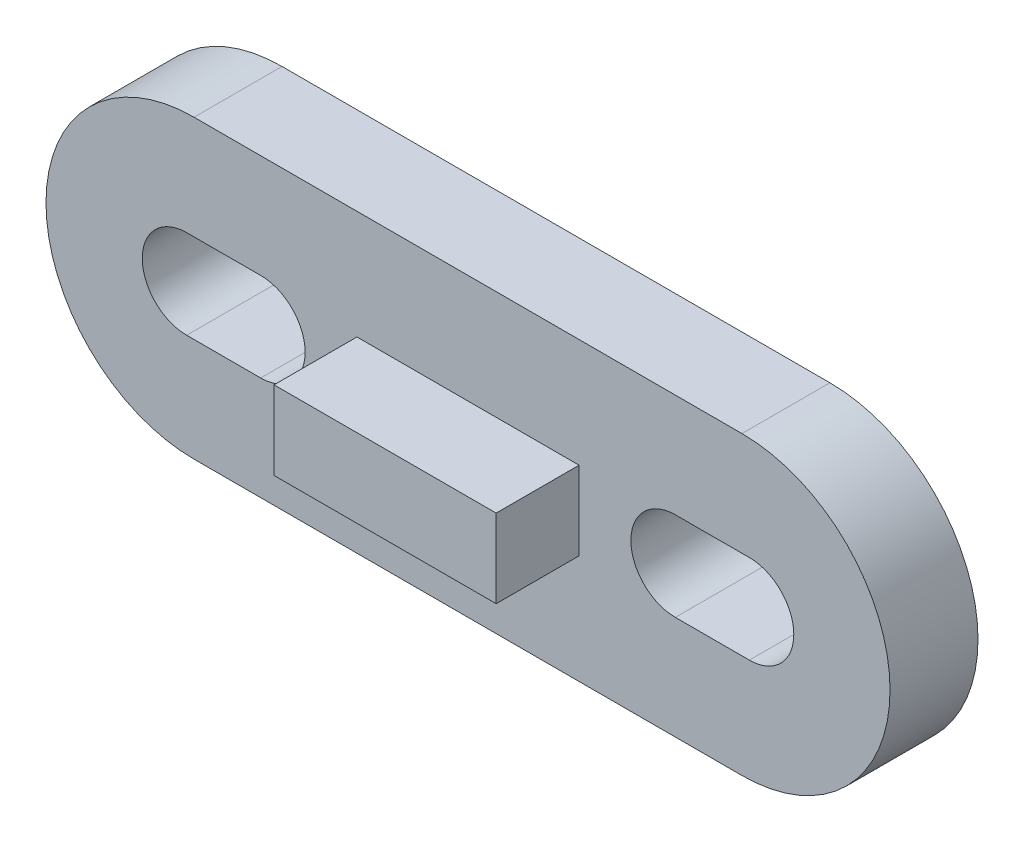
SolidWorks part; units mm, degrees
ref_plane "Front Plane" through (0, 0, 0) normal (0, 0, 1) x (1, 0, 0)
ref_plane "Top Plane" through (0, 0, 0) normal (0, 1, 0) x (1, 0, 0)
ref_plane "Right Plane" through (0, 0, 0) normal (1, 0, 0) x (0, 0, -1)
sketch "Sketch3" plane through (0, 0, 0) normal (0, 0, 1) x (1, 0, 0)
  line L0 (-9.25, 0) -> (9.25, 0) construction
  line L3 (-9.5, 0) -> (-7, 0) construction
  line L4 (-9.5, 1.5) -> (-7, 1.5)
  line L5 (-9.5, -1.5) -> (-7, -1.5)
  line L6 (9.5, 0) -> (7, 0) construction
  line L9 (-9.25, 5) -> (9.25, 5)
  line L10 (-9.25, -5) -> (9.25, -5)
  line L11 (9.5, -1.5) -> (7, -1.5)
  line L12 (9.5, 1.5) -> (7, 1.5)
  line L13 (5.5, 0) -> (-5.5, 0) construction
  arc A2 (-9.5, 1.5) -> (-9.5, -1.5) centre (-9.5, 0) ccw
  arc A3 (-7, -1.5) -> (-7, 1.5) centre (-7, 0) ccw
  arc A6 (-9.25, 5) -> (-9.25, -5) centre (-9.25, 0) ccw
  arc A7 (9.25, -5) -> (9.25, 5) centre (9.25, 0) ccw
  arc A8 (9.5, -1.5) -> (9.5, 1.5) centre (9.5, 0) ccw
  arc A9 (7, 1.5) -> (7, -1.5) centre (7, 0) ccw
  point P2 (0, 0)
  point P10 (-8.25, 0)
  point P16 (8.25, 0)
  point P21 (0, 0)
  point P23 (-5.5, 0)
  dimension "D2" = 5
  dimension "D3" = 3
  dimension "D5" = 2.5
  dimension "D4" = 1.5
  dimension "D7" = 11
  dimension "D1" = 18.5
  dimension "D6" = 2.5
extrude "Boss-Extrude2" add sketch "Sketch3" along normal blind 2.97
sketch "Sketch5" plane through (0, 0, 2.97) normal (0, 0, 1) x (1, 0, 0)
  line L1 (-3.75, 1.325) -> (3.75, 1.325)
  line L2 (-3.75, 1.325) -> (-3.75, -1.325)
  line L3 (-3.75, -1.325) -> (3.75, -1.325)
  line L4 (3.75, 1.325) -> (3.75, -1.325)
  line L5 (-3.75, 1.325) -> (3.75, -1.325) construction
  line L6 (-3.75, -1.325) -> (3.75, 1.325) construction
  point P0 (0, 0)
  dimension "D1" = 7.5
  dimension "D2" = 2.65
extrude "Boss-Extrude3" add sketch "Sketch5" along normal blind 2.8
